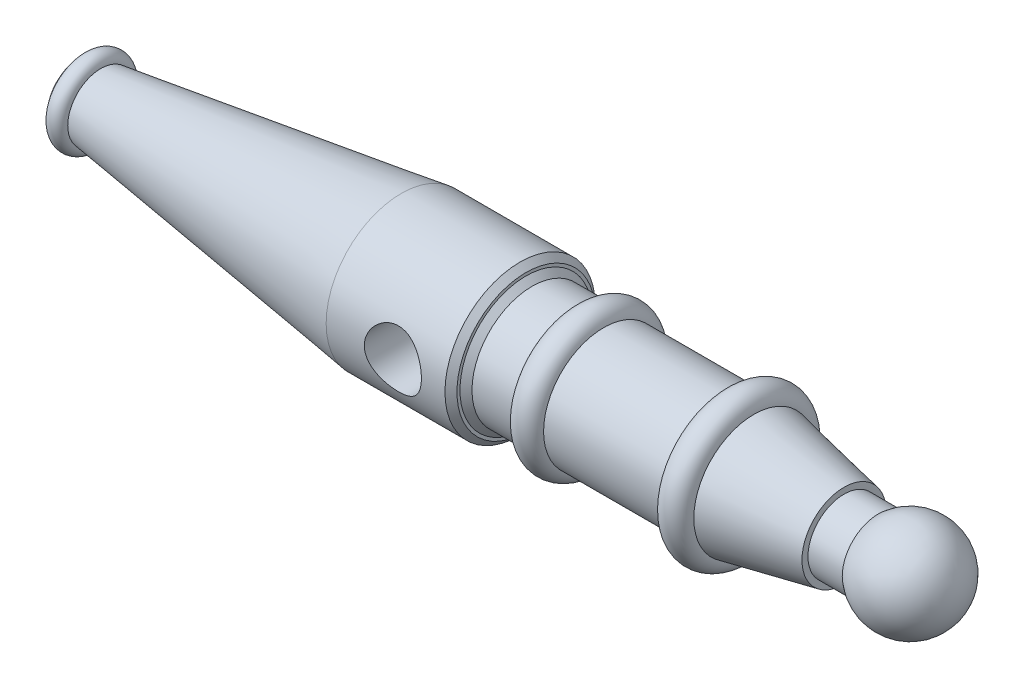
SolidWorks part; units mm, degrees
ref_plane "Front Plane" through (0, 0, 0) normal (0, 0, 1) x (1, 0, 0)
ref_plane "Top Plane" through (0, 0, 0) normal (0, 1, 0) x (1, 0, 0)
ref_plane "Right Plane" through (0, 0, 0) normal (1, 0, 0) x (0, 0, -1)
sketch "Sketch1" plane through (0, 0, 0) normal (0, 0, 1) x (1, 0, 0)
  line L1 (1460.7638, 0) -> (1380.7638, 0) construction
  line L2 (1270.8487, 60) -> (1270.8487, 70)
  line L3 (1270.8487, 60) -> (1327.8487, 60)
  line L7 (1270.8487, 70) -> (1120.8487, 100)
  line L8 (534, 125) -> (34, 55)
  line L9 (1070.8487, 100) -> (870.8487, 100)
  line L10 (0, 55) -> (4, 55)
  line L11 (821.7147, 100) -> (741.7147, 100)
  line L12 (0, 0) -> (1460.7638, 0)
  line L14 (0, 55) -> (0, 0)
  line L16 (4, 55) -> (34, 55) construction
  line L17 (741.7147, 125) -> (741.7147, 100)
  line L18 (741.7147, 125) -> (534, 125)
  line L29 (1460.7638, 0) -> (1459.7639, -0.0169)
  arc A0 (1460.7638, 0) -> (1327.8487, 60) centre (1380.7638, 0) ccw
  arc A1 (1120.8487, 100) -> (1070.8487, 100) centre (1095.8487, 100) ccw
  arc A2 (870.8487, 100) -> (821.7147, 100) centre (846.2817, 95.3674) ccw
  arc A4 (4, 55) -> (34, 55) centre (19, 55) cw
  point P3 (1299.0046, 0)
  point P67 (1329.4852, 45.9778)
  point P68 (1390, 0)
  point P69 (1465.9408, -3)
  point P70 (1472.9458, -3)
  point P71 (1390, 0)
  point P72 (1326.1067, 52.9778)
  dimension "D3" = 57
  dimension "D4" = 80
  dimension "D18" = 25
  dimension "D19" = 25
  dimension "D25" = 4
  dimension "D27" = 15
  dimension "D5" = 25
  dimension "D28" = 25
  dimension "D6" = 57
  dimension "D7" = 125
  dimension "D8" = 100
  dimension "D9" = 50
  dimension "D10" = 200
  dimension "D11" = 100
  dimension "D12" = 80
  dimension "D13" = 100
  dimension "D14" = 70
  dimension "D15" = 60
  dimension "D16" = 55
  dimension "D17" = 150
  dimension "D20" = 55
  dimension "D21" = 500
  dimension "D22" = 125
  dimension "D23" = 25
  dimension "D24" = 741.7147
  dimension "D26" = 30
  dimension "D29" = 129.1341
revolve "Revolve12" add sketch "Sketch1" angle 360 about L12
chamfer "Chamfer1" distance 10 angle 45 2 edges at (741.7147, 0, 125) (741.7147, 0, 100)
sketch "Sketch3" plane through (0, 0, 0) normal (0, 0, 1) x (1, 0, 0)
  line L0 (534, -125) -> (731.7147, -125) construction
  circle A0 centre (645, 0) radius 47.5
  dimension "D1" = 95
  dimension "D2" = 645
  dimension "D3" = 125
extrude "Cut-Extrude2" cut sketch "Sketch3" against normal through all both and the other way through all
sketch "Sketch4" plane through (0, 0, 0) normal (-1, 0, 0) x (0, 0, 1)
  circle A0 centre (0, 0) radius 47.5
  dimension "D1" = 95
extrude "Cut-Extrude3" cut sketch "Sketch4" against normal blind 16 draft 45
sketch "Sketch5" plane through (16, 0, 0) normal (-1, 0, 0) x (0, 0, 1)
  circle A0 centre (0, 0) radius 32
  dimension "D1" = 64
extrude "Cut-Extrude4" cut sketch "Sketch5" against normal blind 375
sketch "Sketch6" plane through (391, 0, 0) normal (-1, 0, 0) x (0, 0, 1)
  circle A0 centre (0, 0) radius 32
  dimension "D1" = 64
extrude "Cut-Extrude5" cut sketch "Sketch6" against normal blind 9 draft 60
sketch "Sketch7" plane through (400, 0, 0) normal (-1, 0, 0) x (0, 0, 1)
  circle A0 centre (0, 0) radius 16
  dimension "D1" = 32
extrude "Cut-Extrude6" cut sketch "Sketch7" against normal blind 93
sketch "Sketch8" plane through (493, 0, 0) normal (-1, 0, 0) x (0, 0, 1)
  circle A0 centre (0, 0) radius 16
extrude "Cut-Extrude7" cut sketch "Sketch8" against normal blind 9 draft 60
